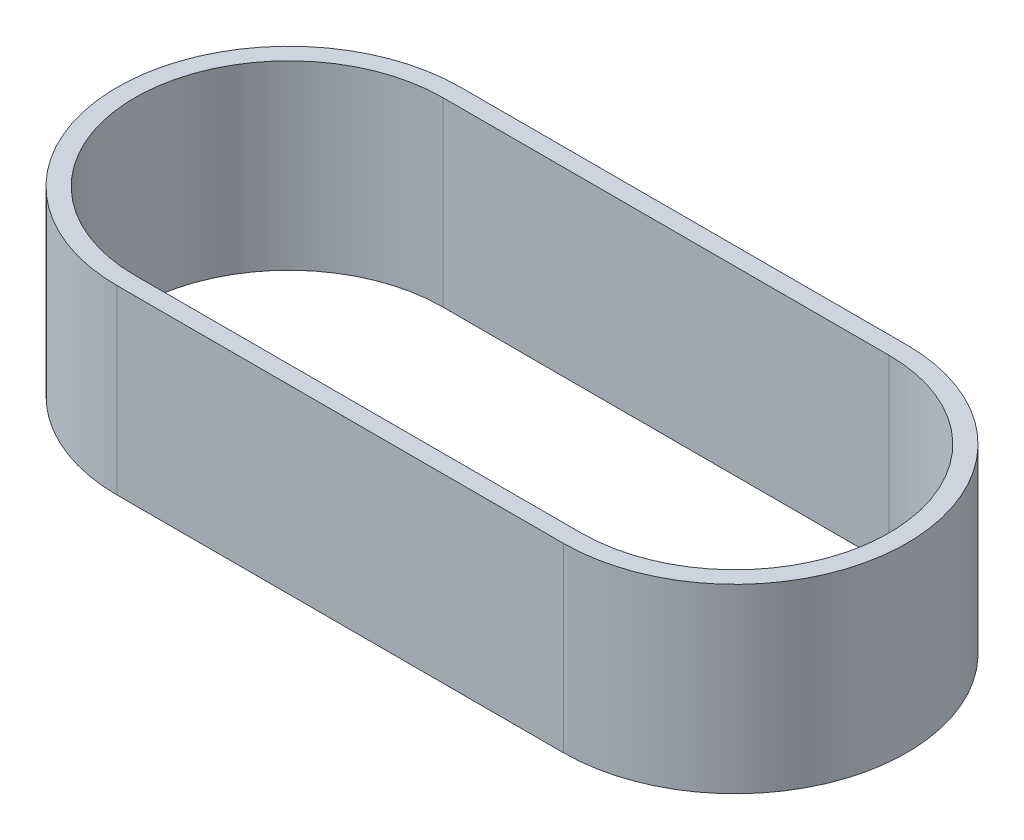
SolidWorks part; units mm, degrees
ref_plane "Front Plane" through (0, 0, 0) normal (0, 0, 1) x (1, 0, 0)
ref_plane "Top Plane" through (0, 0, 0) normal (0, 1, 0) x (1, 0, 0)
ref_plane "Right Plane" through (0, 0, 0) normal (1, 0, 0) x (0, 0, -1)
sketch "Sketch1" plane through (0, 0, 0) normal (0, 1, 0) x (1, 0, 0)
  line L0 (-85.1338, 33.1736) -> (-35.1338, 33.1736) construction
  line L1 (-85.1338, 50.4179) -> (-35.1338, 50.4179)
  line L2 (-85.1338, 15.9294) -> (-35.1338, 15.9294)
  line L3 (-85.1338, 52.4179) -> (-35.1338, 52.4179)
  line L4 (-85.1338, 13.9294) -> (-35.1338, 13.9294)
  arc A0 (-85.1338, 50.4179) -> (-85.1338, 15.9294) centre (-85.1338, 33.1736) ccw
  arc A1 (-35.1338, 15.9294) -> (-35.1338, 50.4179) centre (-35.1338, 33.1736) ccw
  arc A2 (-35.1338, 13.9294) -> (-35.1338, 52.4179) centre (-35.1338, 33.1736) ccw
  arc A3 (-85.1338, 52.4179) -> (-85.1338, 13.9294) centre (-85.1338, 33.1736) ccw
  point P2 (-60.1338, 33.1736)
  dimension "D2" = 50
  dimension "D1" = 2
extrude "Boss-Extrude1" add sketch "Sketch1" along normal blind 20.32
